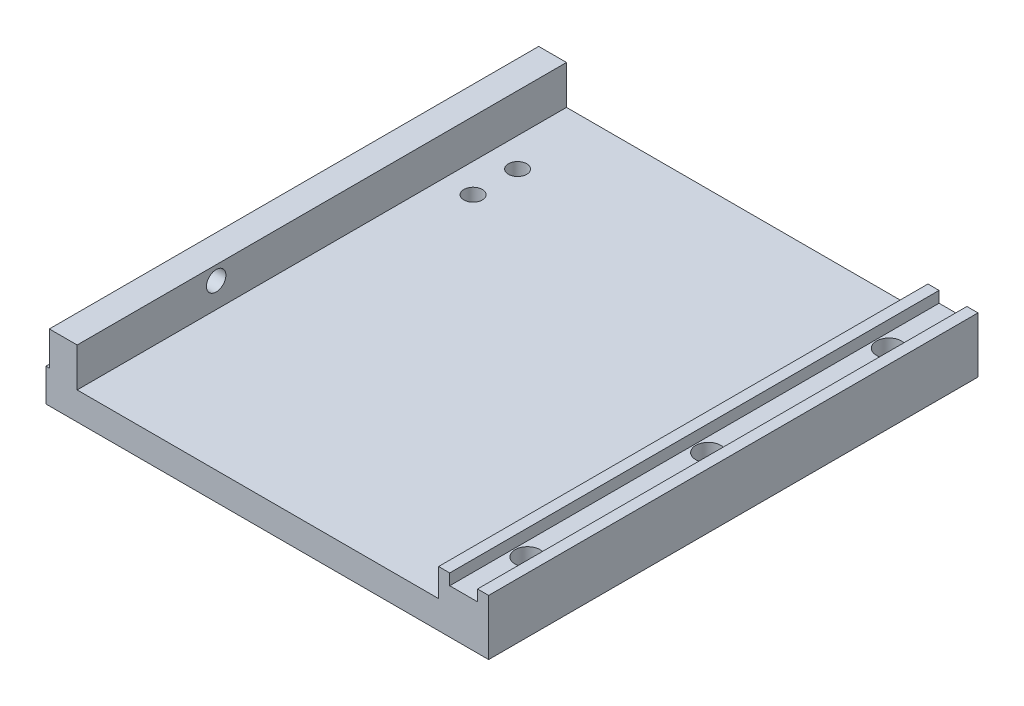
SolidWorks part; units mm, degrees
ref_plane "前视基准面" through (0, 0, 0) normal (0, 0, 1) x (1, 0, 0)
ref_plane "上视基准面" through (0, 0, 0) normal (0, 1, 0) x (1, 0, 0)
ref_plane "右视基准面" through (0, 0, 0) normal (1, 0, 0) x (0, 0, -1)
sketch "草图1" plane through (0, 0, 0) normal (0, 0, 1) x (1, 0, 0)
  line L0 (-9, 10) -> (-9, 5)
  line L1 (-9, 10) -> (-7, 10)
  line L2 (-7, 10) -> (-7, 8)
  line L3 (-7, 8) -> (-2, 8)
  line L4 (-2, 8) -> (-2, 10)
  line L5 (-2, 10) -> (0, 10)
  line L6 (0, 10) -> (0, 0)
  line L7 (-79.6, 0) -> (-79.6, 5.9)
  line L8 (-79.6, 5.9) -> (-79, 5.9)
  line L9 (-79, 5.9) -> (-79, 12)
  line L10 (-74, 12) -> (-79, 12)
  line L11 (-74, 12) -> (-74, 5)
  line L12 (-9, 5) -> (-74, 5)
  line L13 (0, 0) -> (-79.6, 0)
  line L21 (-0.5, 0) -> (-0.5, 4.4) construction
  line L22 (-8.5, 4.4) -> (-8.5, 0) construction
  line L24 (-6.75, 8) -> (-6.75, 4.4) construction
  line L30 (-74, 11.25) -> (-79, 11.25) construction
extrude "凸台-拉伸1" add sketch "草图1" along normal blind 88
hole_wizard "M4 六角凹头螺钉的柱形沉头孔1" positions "草图2" profile "草图3" counterbore size "M4" standard "ISO" end condition through all
sketch "草图2" plane through (0, 0, 0) normal (0, -1, 0) x (-1, 0, 0)
  line L0 (79.6, -44) -> (-18.4609, -44) construction
  line L1 (79.6, -88) -> (79.6, 0) construction
  line L3 (0, -88) -> (0, 0) construction
  point P0 (4.5, -11.5)
  point P2 (4.5, -44)
  point P4 (4.5, -76.5)
  dimension "D1" = 65
  dimension "D2" = 4.5
sketch "草图3" plane through (-4.5, 0, 11.5) normal (1, 0, 0) x (0, 0, -1)
  line L0 (0, 0) -> (0, 12)
  line L1 (0, 12) -> (2.25, 12)
  line L3 (2.25, 12) -> (2.25, 4.4)
  line L4 (2.25, 4.4) -> (4, 4.4)
  line L5 (4, 4.4) -> (4, 0)
  line L7 (4, 0) -> (0, 0)
  line L11 (0, -6.35) -> (0, 107.95) construction
  dimension "通孔孔直径" = 4.5
  dimension "通孔孔深度" = 12
  dimension "柱形沉头孔直径" = 8
  dimension "柱形沉头孔深度" = 4.4
hole_wizard "M4 螺纹孔1" positions "草图4" profile "草图5" tap size "M4" standard "ISO" end condition through all
sketch "草图4" plane through (0, 0, 0) normal (0, -1, 0) x (-1, 0, 0)
  line L0 (0, -88) -> (0, 0) construction
  line L1 (79.6, 0) -> (0, 0) construction
  point P0 (68.8, -14)
  point P2 (68.8, -22)
  dimension "D1" = 68.8
  dimension "D2" = 14
  dimension "D3" = 22
sketch "草图5" plane through (-68.8, 0, 14) normal (1, 0, 0) x (0, 0, -1)
  line L0 (0, 0) -> (0, 12)
  line L1 (0, 12) -> (1.65, 12)
  line L2 (1.65, 12) -> (1.65, 0)
  line L5 (1.65, 0) -> (0, 0)
  line L11 (0, -6.35) -> (0, 107.95) construction
  dimension "通孔螺纹孔钻头直径" = 3.3
  dimension "通孔螺纹孔钻头深度" = 12
cosmetic thread "孔螺蚊线1" parameters "D2"=4
cosmetic thread "孔螺蚊线2" parameters "D2"=4
hole_wizard "M3 螺纹孔1" positions "草图6" profile "草图7" tap size "M3" standard "ISO"
sketch "草图6" plane through (-79.6, 0, 0) normal (-1, 0, 0) x (0, 0, 1)
  line L0 (44, 5.9) -> (44, -5.3544) construction
  line L1 (88, 5.9) -> (0, 5.9) construction
  line L4 (88, 0) -> (0, 0) construction
  point P0 (11.5, 3)
  point P2 (44, 3)
  point P4 (76.5, 3)
  dimension "D1" = 65
  dimension "D2" = 3
cosmetic thread "孔螺蚊线3" parameters "D1"=8, "D2"=3
cosmetic thread "孔螺蚊线4" parameters "D1"=8, "D2"=3
cosmetic thread "孔螺蚊线5" parameters "D1"=8, "D2"=3
sketch "草图7" plane through (-79.6, 3, 11.5) normal (0, 1, 0) x (0, 0, 1)
  line L0 (0, 0) -> (0, 10.2511)
  line L1 (0, 10.2511) -> (1.25, 9.5)
  line L2 (1.25, 9.5) -> (1.25, 0)
  line L5 (1.25, 0) -> (0, 0)
  line L10 (0, 10.2511) -> (-1.25, 9.5) construction
  line L11 (0, -6.35) -> (0, 107.95) construction
  dimension "螺纹孔钻头直径" = 2.5
  dimension "螺纹孔钻头深度" = 9.5
  dimension "导头角度" = 118
sketch "草图8" plane through (-79, 0, 0) normal (-1, 0, 0) x (0, 0, 1)
  line L0 (88, 12) -> (0, 12) construction
  line L1 (0, 12) -> (0, 5.9) construction
  circle A0 centre (63, 9.5) radius 1.75
  dimension "D1" = 3.5
  dimension "D2" = 2.5
  dimension "D3" = 63
extrude "切除-拉伸1" cut sketch "草图8" against normal blind 5
